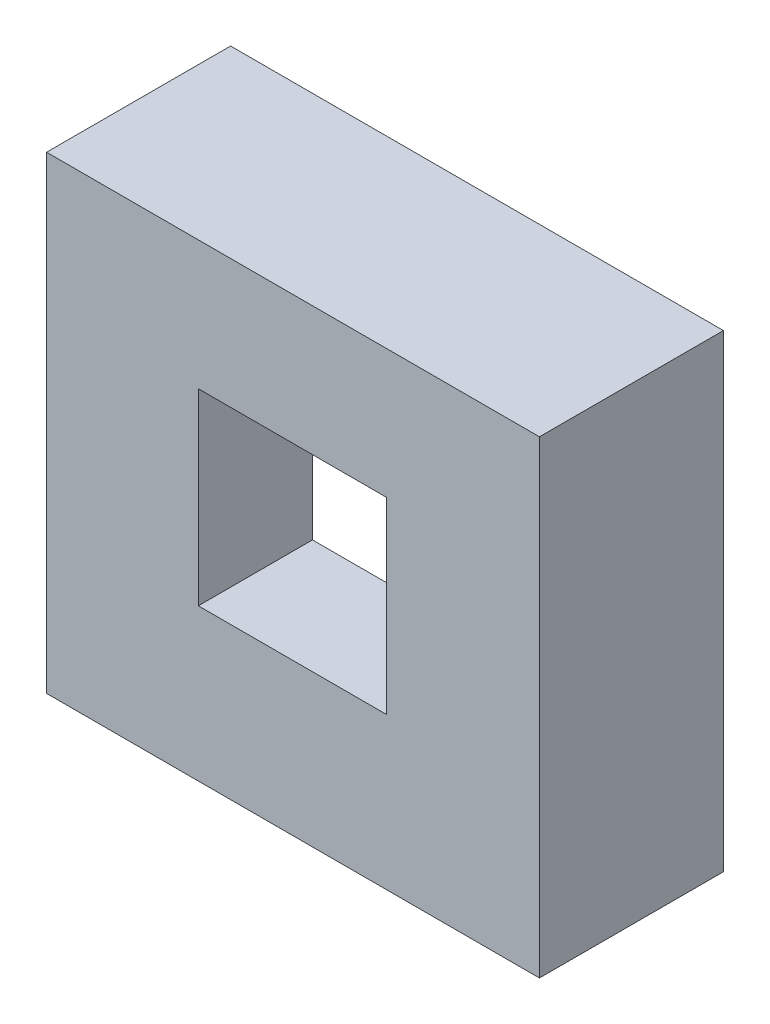
SolidWorks part; units mm, degrees
ref_plane "Front Plane" through (0, 0, 0) normal (0, 0, 1) x (1, 0, 0)
ref_plane "Top Plane" through (0, 0, 0) normal (0, 1, 0) x (1, 0, 0)
ref_plane "Right Plane" through (0, 0, 0) normal (1, 0, 0) x (0, 0, -1)
sketch "Sketch1" plane through (0, 0, 0) normal (0, 0, 1) x (1, 0, 0)
  line L1 (0, 0) -> (36.7, 0)
  line L2 (0, 0) -> (0, 34.9)
  line L3 (0, 34.9) -> (36.7, 34.9)
  line L4 (36.7, 0) -> (36.7, 34.9)
  line L5 (1, 1) -> (35.7, 1)
  line L6 (1, 1) -> (1, 33.9)
  line L7 (1, 33.9) -> (35.7, 33.9)
  line L8 (35.7, 1) -> (35.7, 33.9)
  dimension "D1" = 34.9
  dimension "D2" = 36.7
  dimension "D3" = 1
  dimension "D4" = 1
  dimension "D5" = 1
  dimension "D6" = 1
extrude "Boss-Extrude1" add sketch "Sketch1" along normal blind 11.2
sketch "Sketch2" plane through (0, 0, 0) normal (0, 0, -1) x (-1, 0, 0)
  line L0 (-1, 1) -> (-35.7, 1) construction
  line L1 (-30.7, 1) -> (-25.8, 1)
  line L2 (-30.7, 1) -> (-30.7, 0)
  line L3 (-30.7, 0) -> (-25.8, 0)
  line L4 (-25.8, 1) -> (-25.8, 0)
  line L5 (-36.7, 0) -> (-36.7, 34.9) construction
  line L6 (0, 0) -> (-36.7, 0) construction
  dimension "D1" = 6
  dimension "D2" = 4.9
extrude "Cut-Extrude1" cut sketch "Sketch2" against normal blind 1.9
sketch "Sketch4" plane through (0, 0, 11.2) normal (0, 0, 1) x (1, 0, 0)
  line L1 (36.7, 0) -> (0, 0)
  line L2 (36.7, 0) -> (36.7, 34.9)
  line L3 (36.7, 34.9) -> (0, 34.9)
  line L4 (0, 0) -> (0, 34.9)
extrude "Boss-Extrude3" add sketch "Sketch4" along normal blind 2.5
sketch "Sketch5" plane through (0, 0, 13.7) normal (0, 0, 1) x (1, 0, 0)
  line L8 (36.7, 34.9) -> (0, 34.9) construction
  line L9 (11.3, 25.3) -> (25.3, 25.3)
  line L10 (11.3, 25.3) -> (11.3, 11.3)
  line L11 (11.3, 11.3) -> (25.3, 11.3)
  line L12 (25.3, 25.3) -> (25.3, 11.3)
  line L13 (0, 34.9) -> (0, 0) construction
  dimension "D1" = 9.6
  dimension "D2" = 11.3
  dimension "D5" = 14
  dimension "D6" = 14
extrude "Cut-Extrude2" cut sketch "Sketch5" against normal through all
sketch "Sketch6" plane through (0, 0, 11.2) normal (0, 0, -1) x (-1, 0, 0)
  line L1 (-10.3, 10.3) -> (-26.3, 10.3)
  line L2 (-10.3, 10.3) -> (-10.3, 26.3)
  line L3 (-10.3, 26.3) -> (-26.3, 26.3)
  line L4 (-26.3, 10.3) -> (-26.3, 26.3)
  line L5 (-11.3, 11.3) -> (-25.3, 11.3)
  line L6 (-11.3, 11.3) -> (-11.3, 25.3)
  line L7 (-11.3, 25.3) -> (-25.3, 25.3)
  line L8 (-25.3, 11.3) -> (-25.3, 25.3)
  dimension "D1" = 1
  dimension "D2" = 1
  dimension "D3" = 1
  dimension "D4" = 1
extrude "Boss-Extrude4" add sketch "Sketch6" along normal blind 6
